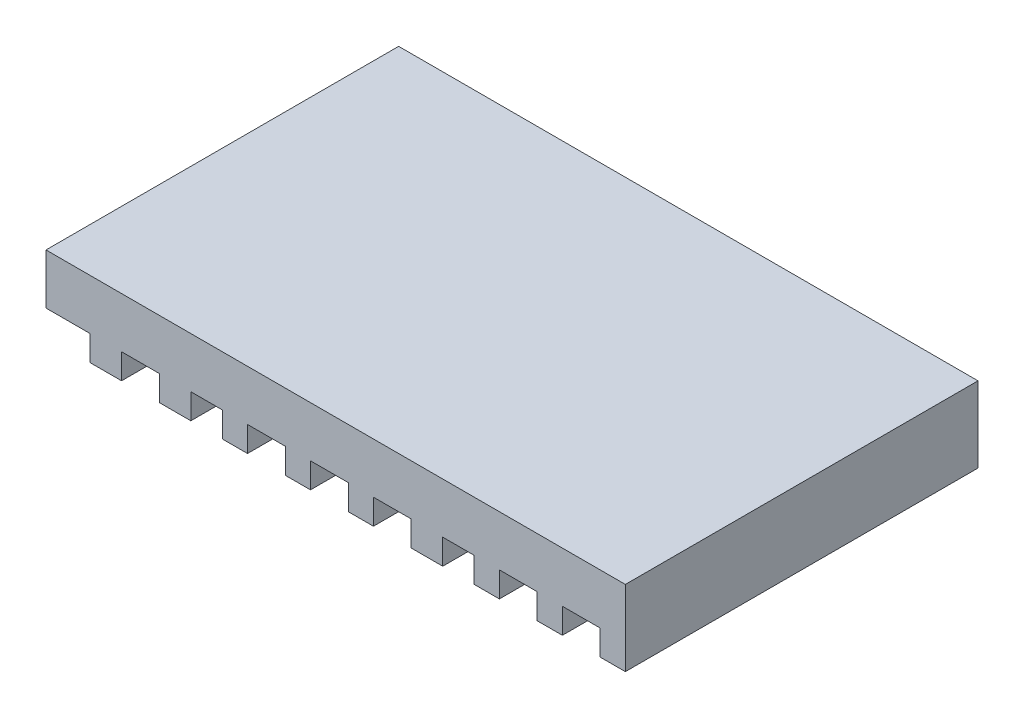
SolidWorks part; units mm, degrees
ref_plane "Front Plane" through (0, 0, 0) normal (0, 0, 1) x (1, 0, 0)
ref_plane "Top Plane" through (0, 0, 0) normal (0, 1, 0) x (1, 0, 0)
ref_plane "Right Plane" through (0, 0, 0) normal (1, 0, 0) x (0, 0, -1)
sketch "Sketch1" plane through (0, 0, 0) normal (0, 0, 1) x (1, 0, 0)
  line L0 (-23, -1) -> (-19.5, -1)
  line L1 (-23, 3) -> (-23, -1)
  line L2 (23, 3) -> (-23, 3)
  line L3 (23, -3) -> (23, 3)
  line L4 (21, -3) -> (23, -3)
  line L5 (21, -1) -> (21, -3)
  line L6 (18, -1) -> (21, -1)
  line L7 (18, -3) -> (18, -1)
  line L8 (16, -3) -> (18, -3)
  line L9 (16, -1) -> (16, -3)
  line L10 (13, -1) -> (16, -1)
  line L11 (13, -3) -> (13, -1)
  line L12 (11, -3) -> (13, -3)
  line L13 (11, -1) -> (11, -3)
  line L14 (8.5, -1) -> (11, -1)
  line L15 (8.5, -3) -> (8.5, -1)
  line L16 (6, -3) -> (8.5, -3)
  line L17 (6, -1) -> (6, -3)
  line L18 (3, -1) -> (6, -1)
  line L19 (3, -3) -> (3, -1)
  line L20 (1, -3) -> (3, -3)
  line L21 (1, -1) -> (1, -3)
  line L22 (-2, -1) -> (1, -1)
  line L23 (-2, -3) -> (-2, -1)
  line L24 (-4, -3) -> (-2, -3)
  line L25 (-4, -1) -> (-4, -3)
  line L26 (-7, -1) -> (-4, -1)
  line L27 (-7, -3) -> (-7, -1)
  line L28 (-9, -3) -> (-7, -3)
  line L29 (-9, -1) -> (-9, -3)
  line L30 (-11.5, -1) -> (-9, -1)
  line L31 (-11.5, -3) -> (-11.5, -1)
  line L32 (-14, -3) -> (-11.5, -3)
  line L33 (-14, -1) -> (-14, -3)
  line L34 (-17, -1) -> (-14, -1)
  line L35 (-17, -3) -> (-17, -1)
  line L36 (-19.5, -3) -> (-17, -3)
  line L37 (-19.5, -1) -> (-19.5, -3)
  dimension "D1" = 1
  dimension "D2" = 3
  dimension "D3" = 6
  dimension "D4" = 8.5
  dimension "D5" = 23
  dimension "D6" = 3
  dimension "D7" = 1
extrude "Boss-Extrude1" add sketch "Sketch1" along normal blind 28
